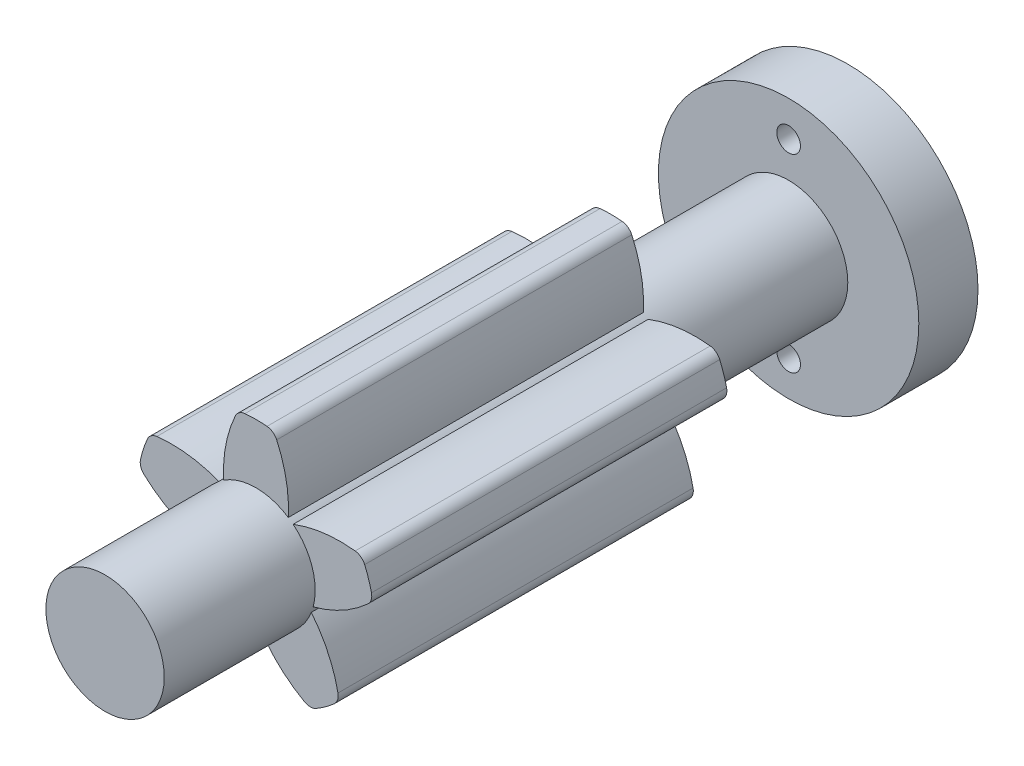
SolidWorks part; units mm, degrees
ref_plane "Plan de face" through (0, 0, 0) normal (0, 0, 1) x (1, 0, 0)
ref_plane "Plan de dessus" through (0, 0, 0) normal (0, 1, 0) x (1, 0, 0)
ref_plane "Plan de droite" through (0, 0, 0) normal (1, 0, 0) x (0, 0, -1)
sketch "Esquisse1" plane through (0, 0, 0) normal (0, 0, 1) x (1, 0, 0)
  circle A0 centre (0, 0) radius 11
  dimension "D1" = 22
extrude "Boss.-Extru.1" add sketch "Esquisse1" along normal blind 5
sketch "Esquisse2" plane through (0, 0, 5) normal (0, 0, 1) x (1, 0, 0)
  line L0 (0, 9.4533) -> (0, -10.2047) construction
  circle A0 centre (0, 0) radius 8
  circle A1 centre (0, 8) radius 1
  circle A2 centre (0, -8) radius 1
  dimension "D1" = 16
  dimension "D2" = 2
extrude "Enlèv. mat.-Extru.1" cut sketch "Esquisse2" against normal through all contours A1 L0 A0 | L0 A1 A0 | L0 A0 A1 | A0 L0 A1 | A2 L0 A0 | L0 A2 A0 | L0 A0 A2 | A0 L0 A2
sketch "Esquisse3" plane through (0, 0, 5) normal (0, 0, 1) x (1, 0, 0)
  circle A0 centre (0, 0) radius 5
  dimension "D1" = 10
extrude "Boss.-Extru.2" add sketch "Esquisse3" along normal blind 57.75
ref_plane "Plan1" through (0, 0, 35) normal (0, 0, 1) x (1, 0, 0)
sketch "Esquisse4" plane through (0, 0, 35) normal (0, 0, 1) x (1, 0, 0)
  line L0 (0, 7) -> (0, 0) construction
  line L1 (-2.5, 7.1206) -> (2.5, 7.1206) construction
  line L2 (0, 0) -> (10, 0) construction
  circle A0 centre (0, 0) radius 5 construction
  circle A1 centre (0, 8) radius 1 construction
  circle A2 centre (0, 0) radius 10 construction
  circle A3 centre (0, 0) radius 5 construction
  arc A4 (-2.7312, 4.1882) -> (-1.5, 9.8869) centre (8.2519, 4.7977) cw
  arc A5 (1.5, 9.8869) -> (2.7312, 4.1882) centre (-8.2519, 4.7977) cw
  arc A6 (-1.5, 9.8869) -> (1.5, 9.8869) centre (0, 0) cw
  circle A8 centre (0, 0) radius 5
  arc A9 (-2.7312, 4.1882) -> (2.7312, 4.1882) centre (0, 0) ccw
  point P11 (0, 5)
  point P13 (5, 0)
  point P14 (10, 0)
  point P20 (-2.5, 7.1206)
  point P21 (2.5, 7.1206)
  dimension "D1" = 11
  dimension "D2" = 5
  dimension "D3" = 5
  dimension "D4" = 3
  dimension "D5" = 0
extrude "Boss.-Extru.3" add sketch "Esquisse4" along normal mid plane 30
fillet "Congé1" radius 1 2 edges at (1.5, 9.8869, 35) (-1.5, 9.8869, 35)
pattern_circular "Répétition circulaire1" count 5 every 72 about axis through (0, 0, 0) along (0, 0, 1) of "Boss.-Extru.3", "Congé1"
